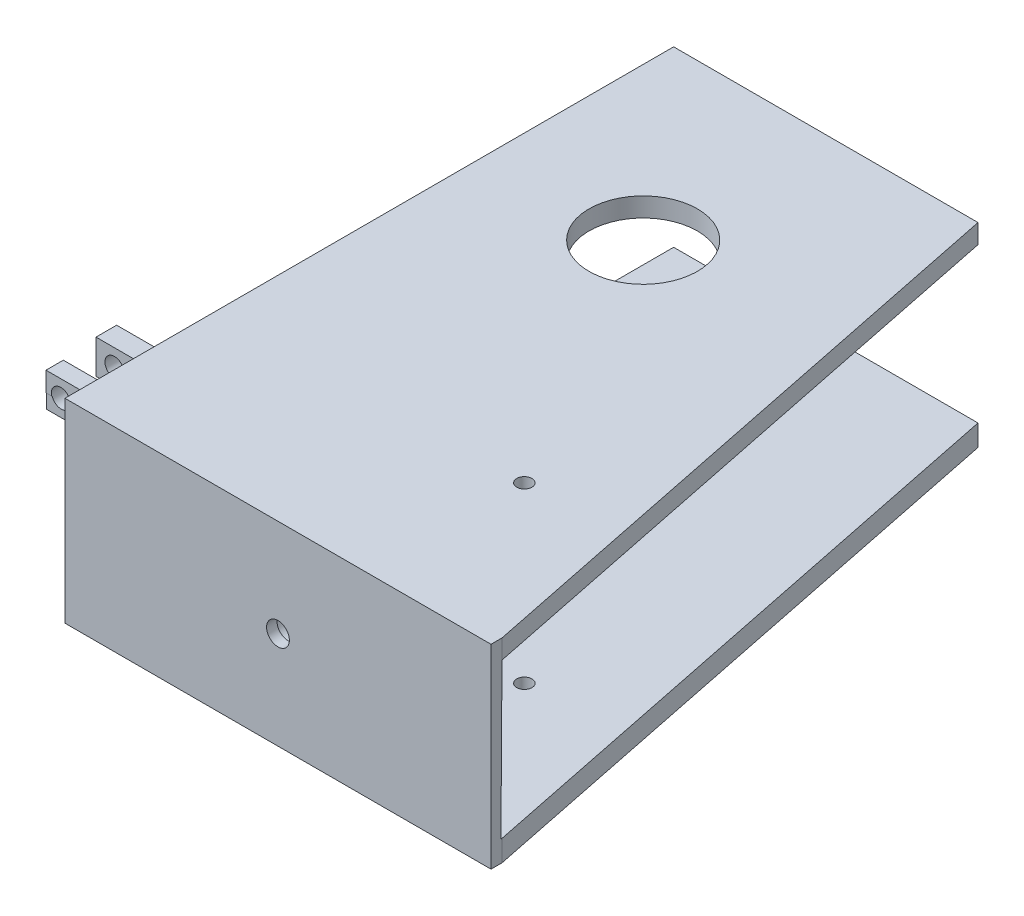
SolidWorks part; units mm, degrees
ref_plane "Alzado" through (0, 0, 0) normal (0, 0, 1) x (1, 0, 0)
ref_plane "Planta" through (0, 0, 0) normal (0, 1, 0) x (1, 0, 0)
ref_plane "Vista lateral" through (0, 0, 0) normal (1, 0, 0) x (0, 0, -1)
sketch "Croquis1" plane through (0, 0, 0) normal (0, 1, 0) x (1, 0, 0)
  line L0 (0, 46.0703) -> (0, -207.9297)
  line L1 (0, 46.0703) -> (127, 46.0703)
  line L2 (0, -207.9297) -> (177.8, -207.9297)
  line L3 (127, 46.0703) -> (177.8, -207.9297)
  dimension "D1" = 254
  dimension "D2" = 127
  dimension "D3" = 177.8
extrude "Saliente-Extruir1" add sketch "Croquis1" along normal blind 4.572
sketch "Croquis2" plane through (0, 0, 0) normal (1, 0, 0) x (0, 0, -1)
  line L1 (-207.9297, 4.572) -> (-207.9297, -71.628)
  line L2 (-207.9297, -71.628) -> (-203.3577, -71.628)
  line L3 (-203.3577, -71.628) -> (-203.3577, 4.572)
  line L4 (46.0703, 4.572) -> (-207.9297, 4.572) construction
  line L5 (-203.3577, 4.572) -> (-207.9297, 4.572)
  dimension "D1" = 76.2
  dimension "D2" = 4.572
extrude "Saliente-Extruir2" add sketch "Croquis2" along normal blind 177.8
sketch "Croquis3" plane through (0, 0, 0) normal (0, 1, 0) x (1, 0, 0)
  line L0 (0, -207.9297) -> (0, 46.0703)
  line L1 (0, 46.0703) -> (127, 46.0703)
  line L2 (127, 46.0703) -> (177.8, -203.3577)
  line L3 (177.8, -203.3577) -> (177.8, -207.9297)
  line L4 (177.8, -207.9297) -> (0, -207.9297)
extrude "Saliente-Extruir3" add sketch "Croquis3" against normal blind 76.2 and the other way blind 5.08
sketch "Croquis4" plane through (0, 0, 0) normal (1, 0, 0) x (0, 0, -1)
  line L0 (46.0703, -2.9195) -> (46.0703, -67.3527)
  line L2 (-203.3577, -2.9195) -> (46.0703, -2.9195)
  line L3 (46.0703, 5.08) -> (46.0703, -76.2) construction
  line L4 (46.0703, -67.3527) -> (-203.7925, -67.3527)
  line L5 (-203.7925, -67.3527) -> (-203.3577, -2.9195)
  line L6 (-203.3577, -76.2) -> (-203.3577, 5.08) construction
extrude "Cortar-Extruir5" cut sketch "Croquis4" along normal blind 208.534
sketch "Croquis5" plane through (0, 0, 0) normal (0, 1, 0) x (1, 0, 0)
  circle A0 centre (63.5, -30.1297) radius 12.7
  dimension "D2" = 25.4
extrude "Cortar-Extruir6" cut sketch "Croquis5" along normal blind 50.038 and the other way blind 148.336
sketch "Croquis6" plane through (0, 0, 0) normal (0, 1, 0) x (1, 0, 0)
  circle A0 centre (63.5, -30.1297) radius 22.606
  dimension "D1" = 45.212
extrude "Cortar-Extruir12" cut sketch "Croquis6" against normal blind 97.282 and the other way blind 33.274
sketch "Croquis7" plane through (0, 0, 0) normal (0, 1, 0) x (1, 0, 0)
  circle A0 centre (122.3529, -133.6568) radius 7.9755
extrude "Cortar-Extruir13" cut sketch "Croquis7" against normal blind 177.8 and the other way blind 66.04
sketch "Croquis8" plane through (0, -76.2, 0) normal (0, -1, 0) x (1, 0, 0)
  circle A0 centre (122.3529, 133.6568) radius 7.9755
  circle A1 centre (122.3529, 133.6568) radius 8.001
  dimension "D1" = 16.002
extrude "Saliente-Extruir8" add sketch "Croquis8" against normal blind 18.034 and the other way blind 19.304
sketch "Croquis9" plane through (0, 5.08, 0) normal (0, 1, 0) x (1, 0, 0)
  circle A0 centre (122.3529, -133.6568) radius 8.001
  dimension "D1" = 16.002
extrude "Saliente-Extruir9" add sketch "Croquis9" against normal blind 19.558 and the other way blind 15.494
sketch "Croquis10" plane through (0, 0, 0) normal (1, 0, 0) x (0, 0, -1)
  line L0 (-141.6578, 20.574) -> (-125.6558, 20.574)
  line L1 (-125.6558, 20.574) -> (-125.6558, 5.08)
  line L2 (-125.6558, 5.08) -> (-141.6578, 5.08)
  line L3 (-203.3577, 5.08) -> (46.0703, 5.08) construction
  line L4 (-141.6578, 5.08) -> (-141.6578, 20.574)
extrude "Cortar-Extruir14" cut sketch "Croquis10" along normal blind 261.874
sketch "Croquis11" plane through (0, 0, 0) normal (1, 0, 0) x (0, 0, -1)
  line L0 (-142.1393, -2.9195) -> (-142.0529, -14.4919)
  line L1 (46.0703, -2.9195) -> (-203.3577, -2.9195) construction
  line L2 (-141.6578, -67.3527) -> (-125.6558, -67.3527)
  line L3 (-125.6558, -67.3527) -> (-125.6558, -57.9972)
  line L4 (-125.6558, -2.9195) -> (-142.1393, -2.9195)
  line L5 (-141.7277, -57.9972) -> (-125.6558, -57.9972)
  line L6 (-142.0529, -14.4919) -> (-125.6558, -14.478)
  line L7 (-141.6578, -14.478) -> (-125.6558, -14.478) construction
  line L8 (-141.7277, -57.9972) -> (-141.6578, -67.3527)
  line L9 (-125.6558, -14.478) -> (-125.6558, -2.9195)
extrude "Cortar-Extruir15" cut sketch "Croquis11" along normal blind 422.402
sketch "Croquis12" plane through (0, 0, 0) normal (0, 1, 0) x (1, 0, 0)
  circle A0 centre (122.3529, -133.6568) radius 8.001
  dimension "D1" = 16.002
extrude "Saliente-Extruir10" add sketch "Croquis12" against normal blind 118.618
sketch "Croquis13" plane through (0, 0, 0) normal (1, 0, 0) x (0, 0, -1)
  line L0 (-141.6578, -67.3527) -> (-125.6558, -67.3527)
  line L1 (-125.6558, -67.3527) -> (-125.6558, -2.9195)
  line L2 (-125.6558, -2.9195) -> (-141.6578, -2.9195)
  line L3 (-141.6578, -2.9195) -> (-141.6578, -67.3527)
extrude "Cortar-Extruir16" cut sketch "Croquis13" along normal blind 300.99
sketch "Croquis14" plane through (0, 0, 0) normal (1, 0, 0) x (0, 0, -1)
  line L0 (-141.8231, -76.2) -> (-141.6578, -118.618)
  line L1 (-203.3577, -76.2) -> (46.0703, -76.2) construction
  line L2 (-141.6578, -118.618) -> (-125.6558, -118.618)
  line L3 (-125.6558, -118.618) -> (-125.6558, -76.2)
  line L4 (-125.6558, -76.2) -> (-141.8231, -76.2)
extrude "Cortar-Extruir17" cut sketch "Croquis14" along normal blind 262.89
sketch "Croquis15" plane through (0, 0, 0) normal (0, 1, 0) x (1, 0, 0)
  circle A0 centre (126.4148, -142.6404) radius 3.175
  dimension "D1" = 6.35
extrude "Cortar-Extruir18" cut sketch "Croquis15" along normal blind 120.142 and the other way blind 292.1
sketch "Croquis16" plane through (0, 0, 0) normal (0, 0, 1) x (1, 0, 0)
  circle A0 centre (88.9, -35.56) radius 4.7625
  dimension "D1" = 9.525
extrude "Cortar-Extruir20" cut sketch "Croquis16" along normal blind 446.532
sketch "Croquis20" plane through (0, 0, 0) normal (0, 0, 1) x (1, 0, 0)
  circle A0 centre (88.9, -35.56) radius 9.0232
  circle A1 centre (88.9, -35.56) radius 5.4139
extrude "Saliente-Extruir12" add sketch "Croquis20" along normal blind 206.502 and the other way blind 2.54
sketch "Croquis22" plane through (0, 0, 0) normal (1, 0, 0) x (0, 0, -1)
  line L0 (2.54, -44.5832) -> (2.54, -26.5368)
  line L2 (-203.6389, -44.5832) -> (2.54, -44.5832) construction
  line L3 (-182.2787, -44.5832) -> (-182.2787, -26.5368)
  line L4 (2.54, -26.5368) -> (-203.5171, -26.5368) construction
  line L5 (-182.2787, -26.5368) -> (2.54, -26.5368)
  line L6 (2.54, -44.5832) -> (-182.2787, -44.5832)
extrude "Cortar-Extruir21" cut sketch "Croquis22" along normal blind 252.984
sketch "Croquis23" plane through (0, 0, 0) normal (1, 0, 0) x (0, 0, -1)
  line L0 (-182.2787, -26.5368) -> (-182.2787, -44.5832)
  line L1 (-182.2787, -44.5832) -> (-192.9588, -44.5832)
  line L2 (-203.6389, -44.5832) -> (-182.2787, -44.5832) construction
  line L3 (-192.9588, -44.5832) -> (-192.9588, -26.5368)
  line L4 (-192.9588, -26.5368) -> (-182.2787, -26.5368)
extrude "Cortar-Extruir22" cut sketch "Croquis23" along normal blind 336.55
sketch "Croquis24" plane through (0, 0, 0) normal (1, 0, 0) x (0, 0, -1)
  line L0 (-193.7291, -2.9195) -> (-193.7291, -11.1058)
  line L1 (46.0703, -2.9195) -> (-203.3577, -2.9195) construction
  line L2 (-193.7291, -11.1058) -> (-186.4962, -11.1058)
  line L3 (-186.4962, -11.1058) -> (-186.4962, -2.9195)
  line L4 (-186.4962, -2.9195) -> (-193.7291, -2.9195)
extrude "Saliente-Extruir13" add sketch "Croquis24" against normal blind 22.098 and the other way blind 23.876
sketch "Croquis25" plane through (0, 0, 0) normal (0, 0, 1) x (1, 0, 0)
  line L0 (-22.098, -11.1058) -> (-22.098, -17.1277)
  line L1 (-22.098, -17.1277) -> (23.876, -17.1277)
  line L2 (23.876, -17.1277) -> (23.876, -11.1058)
  line L3 (23.876, -11.1058) -> (-22.098, -11.1058)
extrude "Saliente-Extruir14" add sketch "Croquis25" along normal blind 193.548 and the other way blind 5.08
sketch "Croquis26" plane through (0, 0, 0) normal (1, 0, 0) x (0, 0, -1)
  line L0 (-186.4962, -11.1058) -> (-186.4962, -17.1277)
  line L1 (5.08, -17.1277) -> (-193.548, -17.1277) construction
  line L2 (-186.4962, -17.1277) -> (5.08, -17.1277)
  line L3 (5.08, -17.1277) -> (5.08, -11.1058)
  line L4 (5.08, -11.1058) -> (-186.4962, -11.1058)
extrude "Cortar-Extruir23" cut sketch "Croquis26" along normal blind 184.658 and the other way blind 81.534
sketch "Croquis27" plane through (0, 0, 0) normal (1, 0, 0) x (0, 0, -1)
  line L0 (-162.7308, -2.9195) -> (-162.7308, -17.1277)
  line L1 (46.0703, -2.9195) -> (-186.4962, -2.9195) construction
  line L2 (-162.7308, -17.1277) -> (-171.3414, -17.1277)
  line L3 (-171.3414, -17.1277) -> (-171.3414, -2.9195)
  line L4 (-171.3414, -2.9195) -> (-162.7308, -2.9195)
extrude "Saliente-Extruir15" add sketch "Croquis27" against normal blind 23.622 and the other way blind 22.86
sketch "Croquis28" plane through (0, 0, 0) normal (0, 0, 1) x (1, 0, 0)
  circle A0 centre (-15.9116, -10.0236) radius 3.9726
  dimension "D1" = 7.9451
extrude "Cortar-Extruir24" cut sketch "Croquis28" along normal blind 207.01
